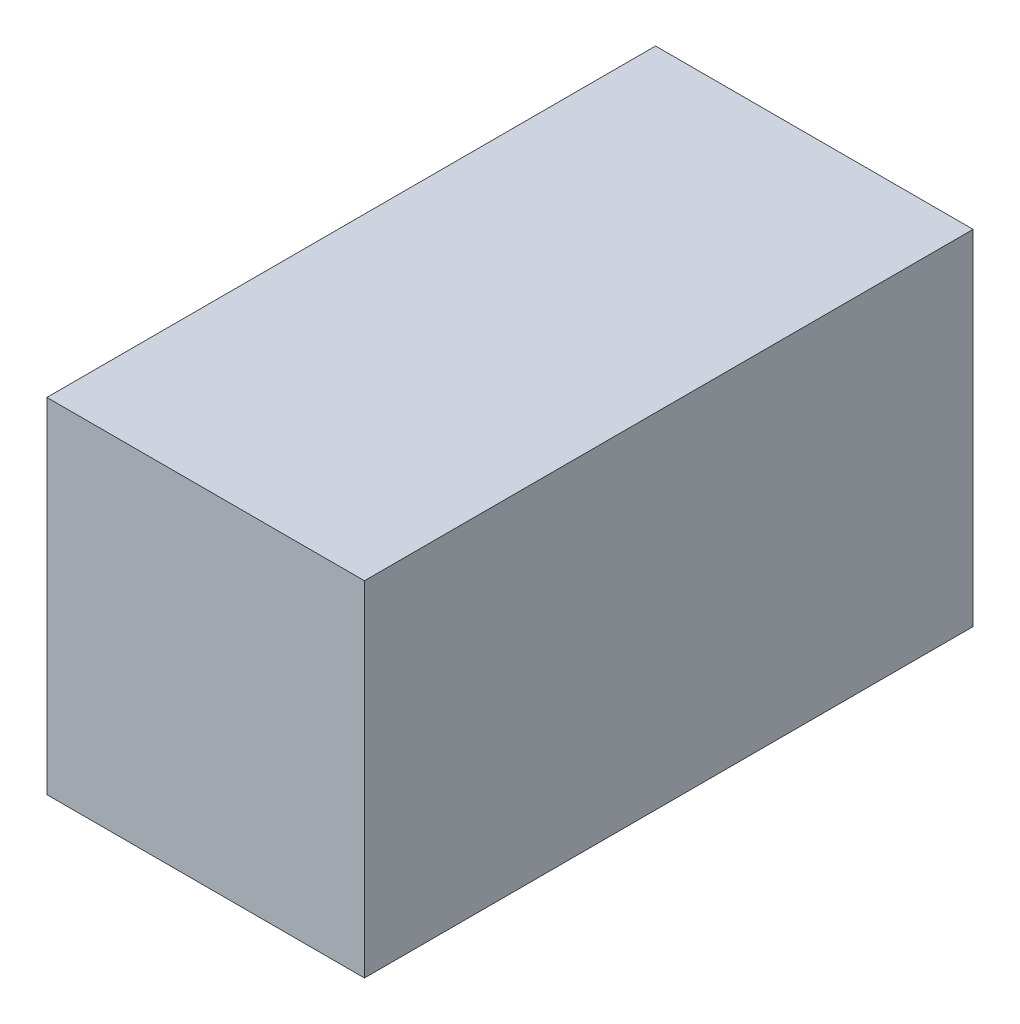
SolidWorks part; units mm, degrees
ref_plane "Front Plane" through (0, 0, 0) normal (0, 0, 1) x (1, 0, 0)
ref_plane "Top Plane" through (0, 0, 0) normal (0, 1, 0) x (1, 0, 0)
ref_plane "Right Plane" through (0, 0, 0) normal (1, 0, 0) x (0, 0, -1)
sketch "Sketch1" plane through (0, 0, 0) normal (0, 1, 0) x (1, 0, 0)
  line L1 (12, -23) -> (-12, -23)
  line L2 (12, -23) -> (12, 23)
  line L3 (12, 23) -> (-12, 23)
  line L4 (-12, -23) -> (-12, 23)
  line L5 (12, -23) -> (-12, 23) construction
  line L6 (12, 23) -> (-12, -23) construction
  point P0 (0, 0)
  dimension "D1" = 24
  dimension "D2" = 46
extrude "Boss-Extrude1" add sketch "Sketch1" along normal blind 26
